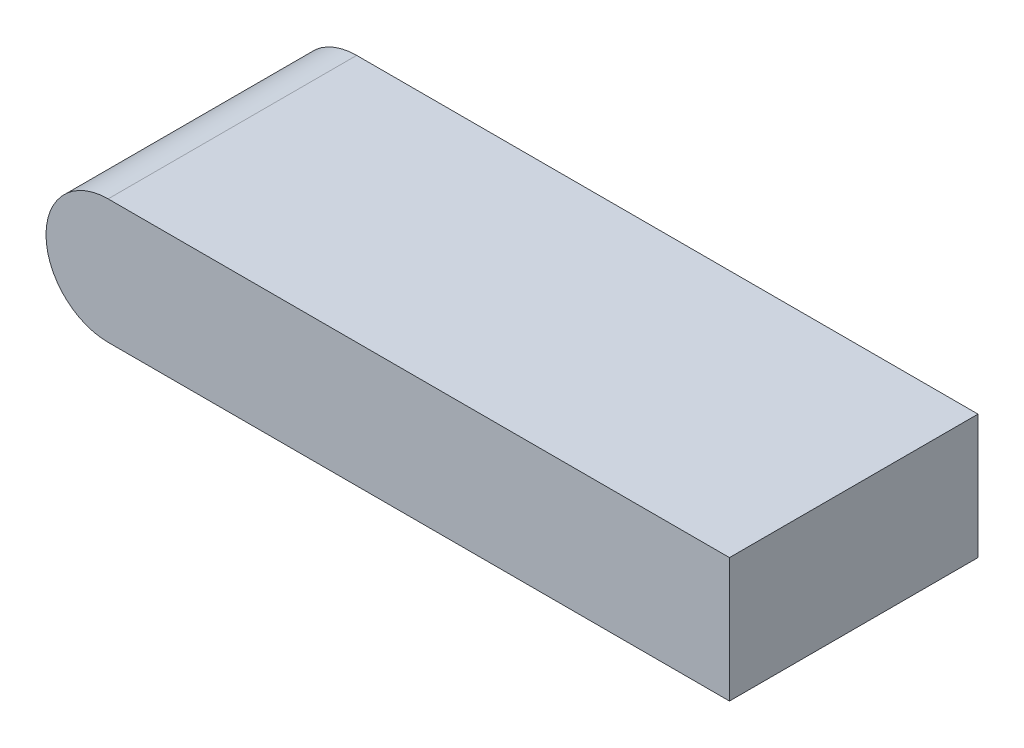
SolidWorks part; units mm, degrees
ref_plane "Front" through (0, 0, 0) normal (0, 0, 1) x (1, 0, 0)
ref_plane "Top" through (0, 0, 0) normal (0, 1, 0) x (1, 0, 0)
ref_plane "Right" through (0, 0, 0) normal (1, 0, 0) x (0, 0, -1)
sketch "草图1" plane through (0, 0, 0) normal (0, 1, 0) x (1, 0, 0)
  line L1 (-12, 4) -> (8, 4)
  line L2 (-12, 4) -> (-12, -4)
  line L3 (-12, -4) -> (8, -4)
  line L4 (8, 4) -> (8, -4)
  dimension "D1" = 8
  dimension "D2" = 20
  dimension "D3" = 8
  dimension "D4" = 4
extrude "凸台-拉伸1" add sketch "草图1" along normal blind 4
sketch "草图2" plane through (0, 0, 4) normal (0, 0, 1) x (1, 0, 0)
  line L0 (-12, 4) -> (-12, 0) construction
  circle A0 centre (-12, 2) radius 2
extrude "凸台-拉伸2" add sketch "草图2" against normal blind 8
